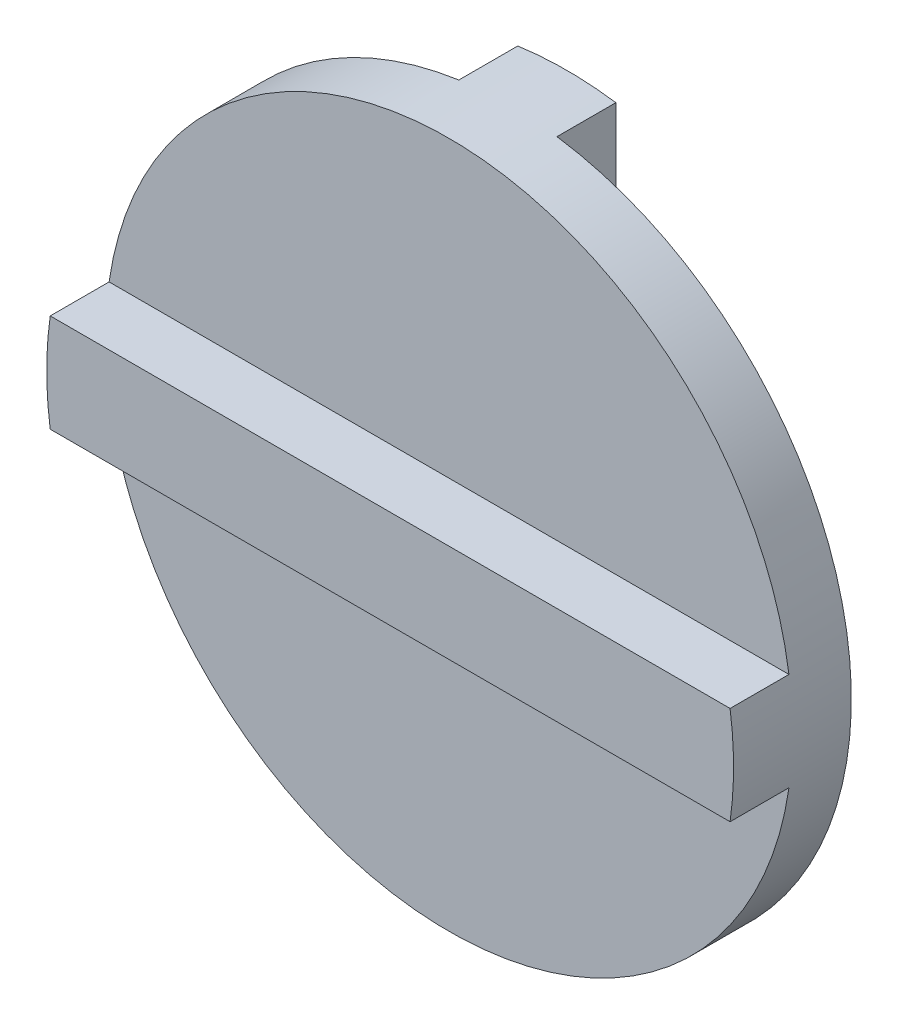
SolidWorks part; units mm, degrees
ref_plane "Front" through (0, 0, 0) normal (0, 0, 1) x (1, 0, 0)
ref_plane "Top" through (0, 0, 0) normal (0, 1, 0) x (1, 0, 0)
ref_plane "Right" through (0, 0, 0) normal (1, 0, 0) x (0, 0, -1)
sketch "Sketch1" plane through (0, 0, 0) normal (0, 0, 1) x (1, 0, 0)
  circle A0 centre (0, 0) radius 17.5
  dimension "D1" = 35
extrude "Boss-Extrude1" add sketch "Sketch1" along normal blind 3 contours A0
sketch "Sketch2" plane through (0, 0, 3) normal (0, 0, 1) x (1, 0, 0)
  line L0 (-17.5208, 2.5) -> (17.5208, 2.5)
  line L2 (0, 2.5) -> (0, -2.5)
  line L3 (-17.5208, -2.5) -> (17.5208, -2.5)
  line L4 (17.5208, 2.5) -> (17.5208, -2.5)
  line L5 (-17.5208, 2.5) -> (-17.5208, -2.5)
  point P0 (17.5208, 0)
  point P6 (-17.5208, 0)
  circle M7 centre (0, 0) radius 17.5
  dimension "D2" = 2.5
  dimension "D3" = 2.5
extrude "Boss-Extrude2" add sketch "Sketch2" along normal blind 3 contours L2 L3 L0 M7 | L3 L2 L0 M7
sketch "Sketch3" plane through (0, 0, 0) normal (0, 0, -1) x (-1, 0, 0)
  line L0 (-2.5, 17.5) -> (-2.5, -17.5)
  line L1 (-2.5, 17.5) -> (2.5, 17.5)
  line L2 (0, 17.5) -> (0, -17.5)
  line L3 (-2.5, -17.5) -> (2.5, -17.5)
  line L4 (2.5, 17.5) -> (2.5, -17.5)
  arc A0 (17.3205, 2.5) -> (-17.3205, 2.5) centre (0, 0) ccw construction
  circle M5 centre (0, 0) radius 17.5
  dimension "D1" = 35
  dimension "D2" = 2.5
extrude "Boss-Extrude3" add sketch "Sketch3" along normal blind 3 contours L2 L0 M5 | L4 L2 M5
